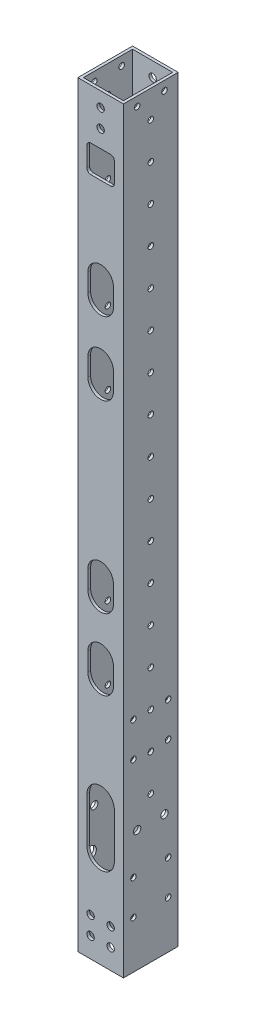
SolidWorks part; units mm, degrees
material "6063-T5"
ref_plane "前视基准面" through (0, 0, 0) normal (0, 0, 1) x (1, 0, 0)
ref_plane "上视基准面" through (0, 0, 0) normal (0, 1, 0) x (1, 0, 0)
ref_plane "右视基准面" through (0, 0, 0) normal (1, 0, 0) x (0, 0, -1)
other "Configuration Table"
sketch "草图2" plane through (0, 0, 0) normal (0, 1, 0) x (1, 0, 0)
  line L1 (-12.5, -15) -> (12.5, -15)
  line L2 (-12.5, -15) -> (-12.5, 15)
  line L3 (-12.5, 15) -> (12.5, 15)
  line L4 (12.5, -15) -> (12.5, 15)
  line L5 (-12.5, -15) -> (12.5, 15) construction
  line L6 (-12.5, 15) -> (12.5, -15) construction
  point P0 (0, 0)
  dimension "D1" = 25
  dimension "D2" = 30
extrude "凸台-拉伸1" add sketch "草图2" along normal mid plane 415
sketch "草图3" plane through (0, 0, 0) normal (0, 1, 0) x (1, 0, 0)
  line L8 (11, -13.5) -> (11, 13.5)
  line L9 (11, 13.5) -> (-11, 13.5)
  line L10 (-11, 13.5) -> (-11, -13.5)
  line L11 (-11, -13.5) -> (11, -13.5)
  line L12 (11, -13.5) -> (11, 13.5)
  line L13 (11, 13.5) -> (-11, 13.5)
  line L14 (-11, 13.5) -> (-11, -13.5)
  line L15 (-11, -13.5) -> (11, -13.5)
  dimension "D1" = 1.5
extrude "切除-拉伸1" cut sketch "草图3" against normal through all both and the other way through all
sketch "草图4" plane through (-12.5, 0, 0) normal (-1, 0, 0) x (0, 0, 1)
  line L0 (-15, -207.5) -> (15, -207.5) construction
  line L1 (-9.5, -181.5) -> (9.5, -181.5) construction
  line L2 (-9.5, -181.5) -> (-9.5, -162.5) construction
  line L3 (-9.5, -162.5) -> (9.5, -162.5) construction
  line L4 (9.5, -181.5) -> (9.5, -162.5) construction
  line L5 (-9.5, -181.5) -> (9.5, -162.5) construction
  line L6 (-9.5, -162.5) -> (9.5, -181.5) construction
  circle A0 centre (-9.5, -162.5) radius 1.525
  circle A1 centre (9.5, -162.5) radius 1.525
  circle A2 centre (9.5, -181.5) radius 1.525
  circle A3 centre (-9.5, -181.5) radius 1.525
  point P0 (0, -172)
  point P7 (0, -207.5)
  dimension "D3" = 3.05
  dimension "D1" = 19
  dimension "D2" = 26
extrude "切除-拉伸2" cut sketch "草图4" against normal through all both and the other way through all
sketch "草图5" plane through (-12.5, 0, 0) normal (-1, 0, 0) x (0, 0, 1)
  circle A4 centre (-9.5, -162.5) radius 3.15
  circle A5 centre (-9.5, -181.5) radius 3.15
  circle A6 centre (9.5, -162.5) radius 3.15
  circle A7 centre (9.5, -181.5) radius 3.15
  dimension "D1" = 6.3
extrude "切除-拉伸3" cut sketch "草图5" against normal up to next
sketch "草图6" plane through (0, 0, -15) normal (0, 0, -1) x (-1, 0, 0)
  line L0 (-12.5, 207.5) -> (12.5, 207.5) construction
  line L1 (-5, 189.5) -> (5, 189.5) construction
  line L2 (-5, 189.5) -> (-5, 199.5) construction
  line L3 (-5, 199.5) -> (5, 199.5) construction
  line L4 (5, 189.5) -> (5, 199.5) construction
  line L5 (-5, 189.5) -> (5, 199.5) construction
  line L6 (-5, 199.5) -> (5, 189.5) construction
  circle A4 centre (0, 199.5) radius 2.025
  circle A5 centre (0, 189.5) radius 2.025
  point P0 (0, 194.5)
  dimension "D3" = 4.05
  dimension "D1" = 10
  dimension "D2" = 10
  dimension "D4" = 8
extrude "切除-拉伸4" cut sketch "草图6" against normal through all
sketch "草图7" plane through (0, 0, -15) normal (0, 0, -1) x (-1, 0, 0)
  line L0 (-12.5, -207.5) -> (12.5, -207.5) construction
  line L1 (-5.5, -196.5) -> (5.5, -196.5) construction
  line L2 (-5.5, -196.5) -> (-5.5, -186.5) construction
  line L3 (-5.5, -186.5) -> (5.5, -186.5) construction
  line L4 (5.5, -196.5) -> (5.5, -186.5) construction
  line L5 (-5.5, -196.5) -> (5.5, -186.5) construction
  line L6 (-5.5, -186.5) -> (5.5, -196.5) construction
  circle A0 centre (5.5, -186.5) radius 2.025
  circle A1 centre (5.5, -196.5) radius 2.025
  circle A2 centre (-5.5, -196.5) radius 2.025
  circle A3 centre (-5.5, -186.5) radius 2.025
  point P0 (0, -191.5)
  dimension "D2" = 4.05
  dimension "D1" = 10
  dimension "D3" = 11
  dimension "D4" = 11
extrude "切除-拉伸5" cut sketch "草图7" against normal through all both and the other way through all
sketch "草图8" plane through (0, 0, 15) normal (0, 0, 1) x (1, 0, 0)
  line L5 (-5.5, -186.5) -> (5.5, -186.5) construction
  line L6 (-5.5, -186.5) -> (-5.5, -196.5) construction
  line L7 (-5.5, -196.5) -> (5.5, -196.5) construction
  line L8 (5.5, -186.5) -> (5.5, -196.5) construction
  circle A4 centre (-5.5, -186.5) radius 4
  circle A5 centre (5.5, -186.5) radius 4
  circle A6 centre (5.5, -196.5) radius 4
  circle A7 centre (-5.5, -196.5) radius 4
  dimension "D1" = 8
extrude "切除-拉伸7" cut sketch "草图8" along normal up to surface (1.5 mm away) from surface at -30 up to face at (3.475, -186.5, -13.5) starting at face at (7.525, -186.5, -15)
sketch "草图9" plane through (-12.5, 0, 0) normal (-1, 0, 0) x (0, 0, 1)
  circle A0 centre (-9.5, -87.5) radius 1.525
  circle A1 centre (-9.5, -106.5) radius 1.525
  circle A2 centre (9.5, -87.5) radius 1.525
  circle A3 centre (9.5, -106.5) radius 1.525
  circle A4 centre (-9.5, -87.5) radius 1.5 construction
  circle A5 centre (-9.5, -106.5) radius 1.5 construction
  circle A6 centre (9.5, -106.5) radius 1.5 construction
  circle A7 centre (9.5, -87.5) radius 1.5 construction
  dimension "D1" = 3.05
extrude "切除-拉伸8" cut sketch "草图9" against normal through all
sketch "草图10" plane through (-12.5, 0, 0) normal (-1, 0, 0) x (0, 0, 1)
  circle A0 centre (-9.5, -87.5) radius 3
  circle A1 centre (-9.5, -106.5) radius 3
  circle A2 centre (9.5, -87.5) radius 3
  circle A3 centre (9.5, -106.5) radius 3
  dimension "D1" = 6
extrude "切除-拉伸9" cut sketch "草图10" against normal blind 5
sketch "草图11" plane through (-12.5, 0, 0) normal (-1, 0, 0) x (0, 0, 1)
  circle A0 centre (-7.5, 202.5) radius 1.525
  circle A1 centre (7.5, 202.5) radius 1.525
  dimension "D1" = 3.05
extrude "切除-拉伸10" cut sketch "草图11" against normal through all both and the other way through all
sketch "草图12" plane through (-12.5, 0, 0) normal (-1, 0, 0) x (0, 0, 1)
  circle A0 centre (-7.5, -141) radius 2.025
  circle A1 centre (7.5, -141) radius 2.025
  dimension "D1" = 4.05
extrude "切除-拉伸11" cut sketch "草图12" against normal through all both
sketch "草图13" plane through (0, 0, -15) normal (0, 0, -1) x (-1, 0, 0)
  line L0 (0, -155) -> (0, -130) construction
  line L1 (-7.5, -155) -> (-7.5, -130)
  line L2 (7.5, -155) -> (7.5, -130)
  line L3 (-12.5, -207.5) -> (12.5, -207.5) construction
  arc A0 (-7.5, -155) -> (7.5, -155) centre (0, -155) ccw
  arc A1 (7.5, -130) -> (-7.5, -130) centre (0, -130) ccw
  point P3 (0, -142.5)
  point P8 (7.5, -142.5)
  dimension "D1" = 25
  dimension "D2" = 15
  dimension "D3" = 65
extrude "切除-拉伸12" cut sketch "草图13" against normal blind 5
pattern_linear "阵列(线性)1" count 7 spacing 47 along (0, 1, 0) of "切除-拉伸12"
sketch "草图15" plane through (0, 0, -15) normal (0, 0, -1) x (-1, 0, 0)
  line L0 (5.5, 165) -> (-5.5, 165) construction
  line L1 (-7.5, 167) -> (-7.5, 178) construction
  line L2 (-5.5, 180) -> (5.5, 180) construction
  line L3 (7.5, 178) -> (7.5, 167) construction
  line L4 (5.5, 165) -> (-5.5, 165)
  line L5 (-7.5, 167) -> (-7.5, 178)
  line L6 (-5.5, 180) -> (5.5, 180)
  line L7 (7.5, 178) -> (7.5, 167)
  arc A0 (-7.5, 167) -> (-5.5, 165) centre (-5.5, 167) ccw construction
  arc A1 (5.5, 165) -> (7.5, 167) centre (5.5, 167) ccw construction
  arc A2 (-5.5, 180) -> (-7.5, 178) centre (-5.5, 178) ccw construction
  arc A4 (-7.5, 167) -> (-5.5, 165) centre (-5.5, 167) ccw
  arc A5 (5.5, 165) -> (7.5, 167) centre (5.5, 167) ccw
  arc A6 (-5.5, 180) -> (-7.5, 178) centre (-5.5, 178) ccw
  arc A7 (7.5, 178) -> (5.5, 180) centre (5.5, 178) ccw
extrude "切除-拉伸13" cut sketch "草图15" against normal through all both
sketch "草图16" plane through (0, 0, 13.5) normal (0, 0, -1) x (-1, 0, 0)
  line L0 (7.5, -155) -> (7.5, -130) construction
  line L1 (-7.5, -130) -> (-7.5, -155) construction
  line L2 (7.5, -155) -> (7.5, -130)
  line L3 (-7.5, -130) -> (-7.5, -155)
  arc A0 (7.5, -130) -> (-7.5, -130) centre (0, -130) ccw construction
  arc A1 (-7.5, -155) -> (7.5, -155) centre (0, -155) ccw construction
  arc A2 (7.5, -130) -> (-7.5, -130) centre (0, -130) ccw
  arc A3 (-7.5, -155) -> (7.5, -155) centre (0, -155) ccw
extrude "切除-拉伸14" cut sketch "草图16" against normal through all both
sketch "草图17" plane through (0, 0, 15) normal (0, 0, 1) x (1, 0, 0)
  line L0 (7, -62) -> (7, -72) construction
  line L1 (-7, -72) -> (-7, -62) construction
  line L2 (7, -23) -> (7, -33) construction
  line L3 (-7, -33) -> (-7, -23) construction
  line L4 (7, 78) -> (7, 68) construction
  line L5 (-7, 68) -> (-7, 78) construction
  line L6 (7, 118) -> (7, 108) construction
  line L7 (-7, 108) -> (-7, 118) construction
  line L8 (7, -62) -> (7, -72)
  line L9 (-7, -72) -> (-7, -62)
  line L10 (7, -23) -> (7, -33)
  line L11 (-7, -33) -> (-7, -23)
  line L12 (7, 78) -> (7, 68)
  line L13 (-7, 68) -> (-7, 78)
  line L14 (7, 118) -> (7, 108)
  line L15 (-7, 108) -> (-7, 118)
  arc A0 (-7, -72) -> (7, -72) centre (0, -72) ccw construction
  arc A1 (7, -62) -> (-7, -62) centre (0, -62) ccw construction
  arc A2 (-7, -33) -> (7, -33) centre (0, -33) ccw construction
  arc A3 (7, -23) -> (-7, -23) centre (0, -23) ccw construction
  arc A4 (-7, 68) -> (7, 68) centre (0, 68) ccw construction
  arc A5 (7, 78) -> (-7, 78) centre (0, 78) ccw construction
  arc A6 (-7, 108) -> (7, 108) centre (0, 108) ccw construction
  arc A7 (7, 118) -> (-7, 118) centre (0, 118) ccw construction
  arc A8 (-7, -72) -> (7, -72) centre (0, -72) ccw
  arc A9 (7, -62) -> (-7, -62) centre (0, -62) ccw
  arc A10 (-7, -33) -> (7, -33) centre (0, -33) ccw
  arc A11 (7, -23) -> (-7, -23) centre (0, -23) ccw
  arc A12 (-7, 68) -> (7, 68) centre (0, 68) ccw
  arc A13 (7, 78) -> (-7, 78) centre (0, 78) ccw
  arc A14 (-7, 108) -> (7, 108) centre (0, 108) ccw
  arc A15 (7, 118) -> (-7, 118) centre (0, 118) ccw
extrude "切除-拉伸15" cut sketch "草图17" against normal blind 10
sketch "草图18" plane through (-12.5, 0, 0) normal (-1, 0, 0) x (0, 0, 1)
  circle A0 centre (0, -127.5) radius 1.525
  dimension "D1" = 3.05
extrude "切除-拉伸16" cut sketch "草图18" against normal through all both and the other way through all
pattern_linear "阵列(线性)2" count 17 spacing 20 along (0, 1, 0) of "切除-拉伸16"
sketch "草图19" plane through (11, 0, 0) normal (-1, 0, 0) x (0, 0, 1)
  circle A0 centre (0, 152.5) radius 2.025
  circle A1 centre (0, 132.5) radius 2.025
  dimension "D1" = 4.05
